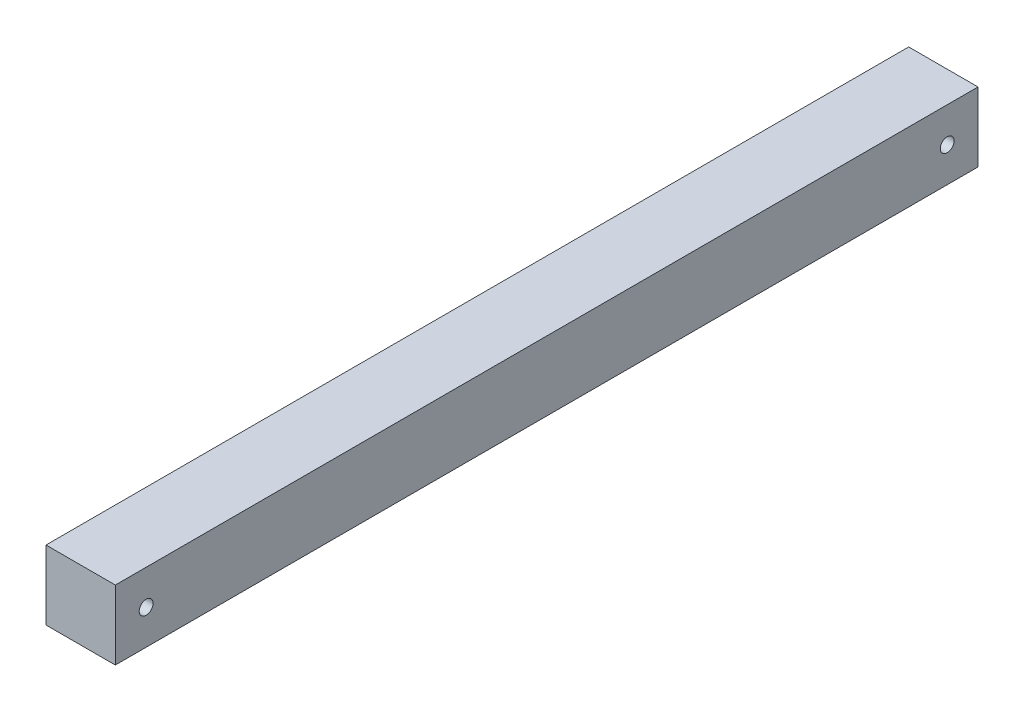
SolidWorks part; units mm, degrees
ref_plane "Plan de face" through (0, 0, 0) normal (0, 0, 1) x (1, 0, 0)
ref_plane "Plan de dessus" through (0, 0, 0) normal (0, 1, 0) x (1, 0, 0)
ref_plane "Plan de droite" through (0, 0, 0) normal (1, 0, 0) x (0, 0, -1)
sketch "Esquisse1" plane through (0, 0, 0) normal (0, 0, 1) x (1, 0, 0)
  line L1 (-27.9906, 19.1427) -> (-5.4906, 19.1427)
  line L2 (-27.9906, 19.1427) -> (-27.9906, -3.3573)
  line L3 (-27.9906, -3.3573) -> (-5.4906, -3.3573)
  line L4 (-5.4906, 19.1427) -> (-5.4906, -3.3573)
  dimension "D1" = 22.5
  dimension "D2" = 22.5
extrude "Boss.-Extru.1" add sketch "Esquisse1" along normal blind 280
sketch "Esquisse2" plane through (-5.4906, 0, 0) normal (1, 0, 0) x (0, 0, -1)
  line L0 (-280, -3.3573) -> (-280, 19.1427) construction
  line L1 (-280, -3.3573) -> (0, -3.3573) construction
  line L2 (-280, 19.1427) -> (0, 19.1427) construction
  line L3 (0, -3.3573) -> (0, 19.1427) construction
  circle A0 centre (-270, 7.8927) radius 2.25
  circle A1 centre (-10, 7.8927) radius 2.25
  point P10 (0, 0)
  point P12 (-14.491, 5.1456)
  dimension "D5" = 4.5
  dimension "D6" = 4.5
  dimension "D1" = 10
  dimension "D2" = 11.25
  dimension "D3" = 11.25
  dimension "D4" = 10
extrude "Enlèv. mat.-Extru.1" cut sketch "Esquisse2" against normal up to next
